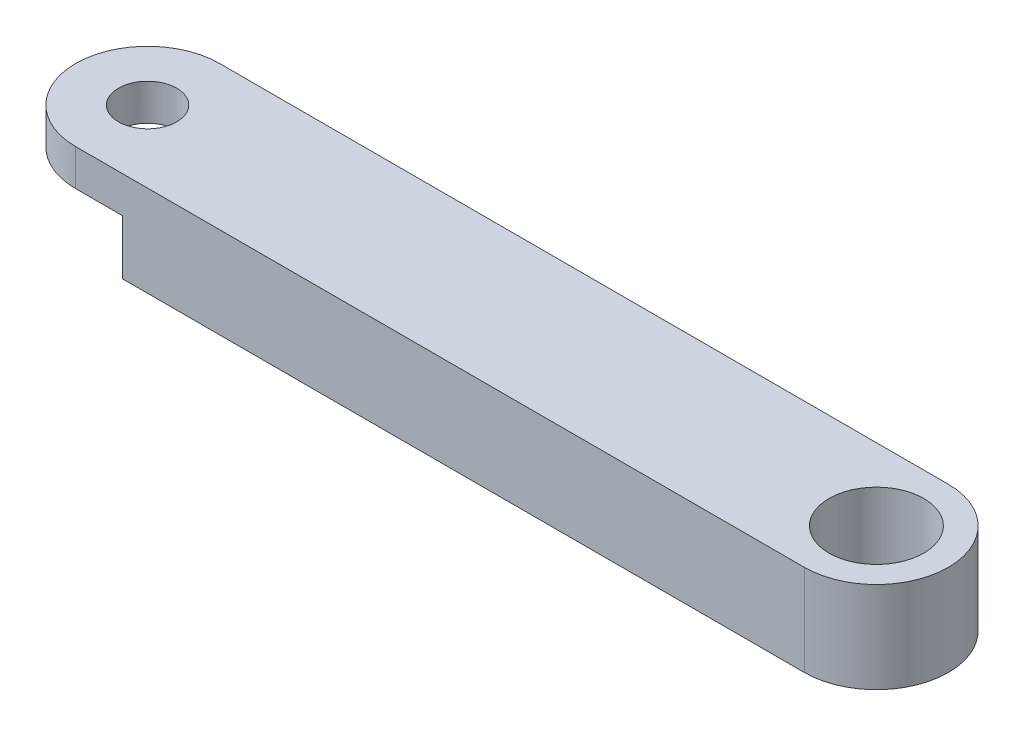
SolidWorks part; units mm, degrees
ref_plane "前视基准面" through (0, 0, 0) normal (0, 0, 1) x (1, 0, 0)
ref_plane "上视基准面" through (0, 0, 0) normal (0, 1, 0) x (1, 0, 0)
ref_plane "右视基准面" through (0, 0, 0) normal (1, 0, 0) x (0, 0, -1)
other "Configuration Table"
sketch "Sketch1" plane through (0, 0, 0) normal (0, 1, 0) x (1, 0, 0)
  line L0 (0, 3.95) -> (40, 3.95)
  line L1 (0, -3.95) -> (40, -3.95)
  arc A0 (0, 3.95) -> (0, -3.95) centre (0, 0) ccw
  circle A1 centre (0, 0) radius 1.6
  arc A2 (40, 3.95) -> (40, -3.95) centre (40, 0) cw
  circle A3 centre (40, 0) radius 2.6
  dimension "D2" = 3.2
  dimension "D5" = 5.2
  dimension "D1" = 7.9
  dimension "D3" = 40
  dimension "D4" = 40
extrude "Boss-Extrude1" add sketch "Sketch1" along normal blind 5
sketch "Sketch2" plane through (0, 0, 0) normal (0, -1, 0) x (1, 0, 0)
  line L3 (2.5695, 3) -> (2.5695, -3)
  line L5 (0, 3.95) -> (40, 3.95) construction
  line L6 (2.5695, 3) -> (2.5695, 3.95)
  line L7 (2.5695, 3.95) -> (0, 3.95)
  line L8 (2.5695, -3) -> (2.5695, -3.95)
  line L9 (40, -3.95) -> (0, -3.95) construction
  line L10 (2.5695, -3.95) -> (0, -3.95)
  circle A1 centre (0, 0) radius 1.6 construction
  arc A2 (0, 3.95) -> (0, -3.95) centre (0, 0) ccw
  circle A7 centre (0, 0) radius 1.6
  dimension "D1" = 6
extrude "Cut-Extrude1" cut sketch "Sketch2" against normal blind 3
